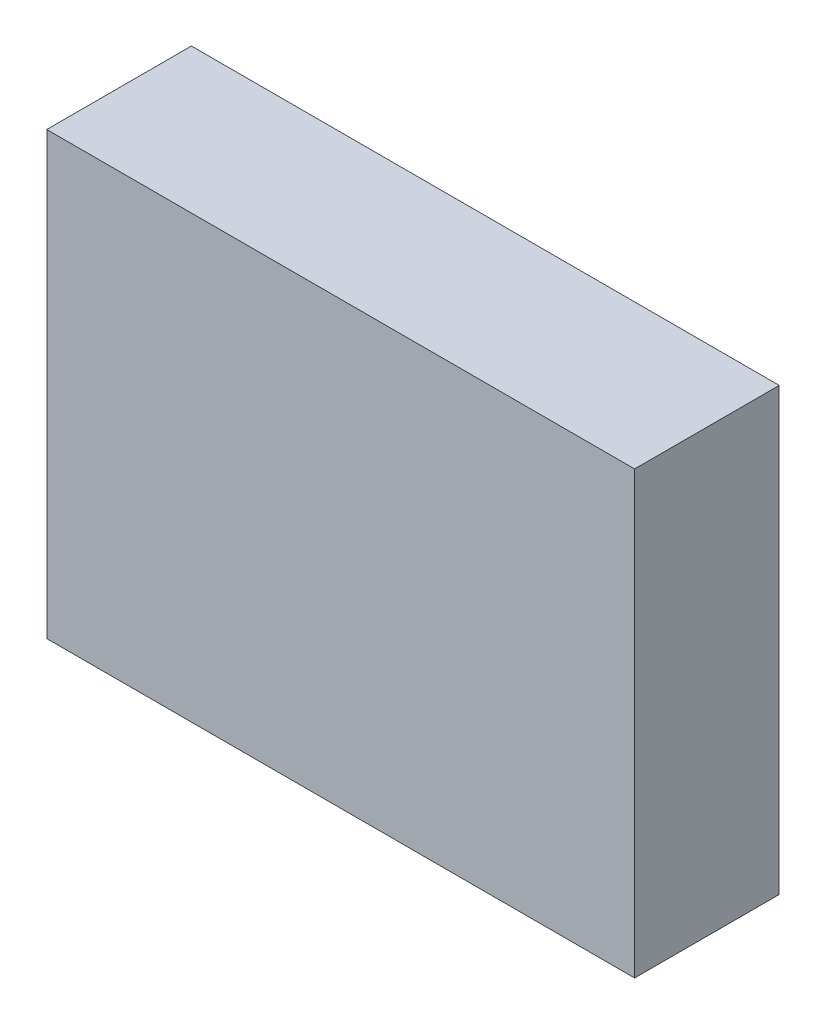
SolidWorks part; units mm, degrees
ref_plane "Front Plane" through (0, 0, 0) normal (0, 0, 1) x (1, 0, 0)
ref_plane "Top Plane" through (0, 0, 0) normal (0, 1, 0) x (1, 0, 0)
ref_plane "Right Plane" through (0, 0, 0) normal (1, 0, 0) x (0, 0, -1)
sketch "Sketch1" plane through (0, 0, 0) normal (0, 0, 1) x (1, 0, 0)
  line L0 (-2.032, 1.524) -> (2.032, 1.524)
  line L1 (2.032, 1.524) -> (2.032, -1.524)
  line L2 (2.032, -1.524) -> (-2.032, -1.524)
  line L3 (-2.032, -1.524) -> (-2.032, 1.524)
extrude "Component_Outline" add sketch "Sketch1" along normal blind 1 separate body
sketch3d "3DSketch1"
  line L0 (0, 0, 0) -> (1, 0, 0)
  line L1 (0, 0, 0) -> (0, 1, 0)
  line L2 (0, 0, 0) -> (0, 0, 1)
  point P0 (0, 0, 0)
